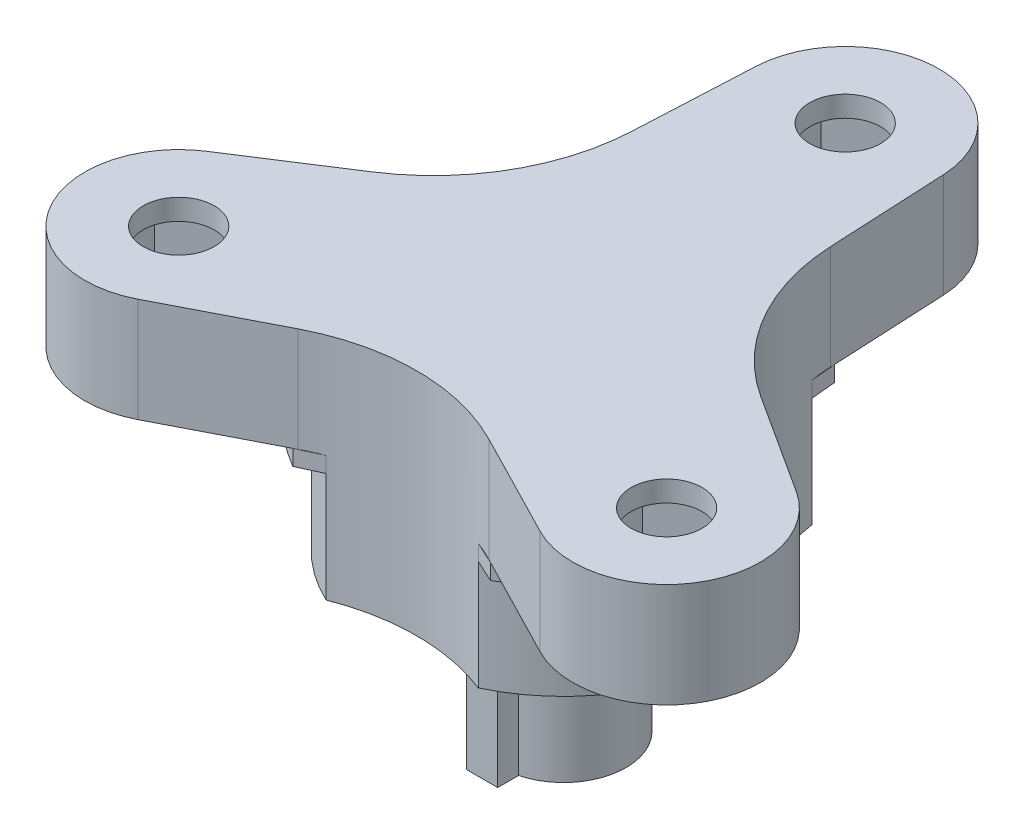
SolidWorks part; units mm, degrees
ref_plane "Ön Düzlem" through (0, 0, 0) normal (0, 0, 1) x (1, 0, 0)
ref_plane "Üst Düzlem" through (0, 0, 0) normal (0, 1, 0) x (1, 0, 0)
ref_plane "Sağ Düzlem" through (0, 0, 0) normal (1, 0, 0) x (0, 0, -1)
sketch "Sketch1" plane through (0, 0, 0) normal (0, 1, 0) x (1, 0, 0)
  line L0 (-4.4946, 13.7195) -> (-4.7723, 8.0342)
  line L1 (0, 13.5) -> (0, 0) construction
  line L2 (4.4946, 13.7195) -> (4.7723, 8.0342)
  line L3 (9.6341, -10.7522) -> (4.5717, -8.15)
  line L4 (14.1287, -2.9673) -> (9.3439, 0.1158)
  line L5 (-14.1287, -2.9673) -> (-9.3439, 0.1158)
  line L6 (-9.6341, -10.7522) -> (-4.5717, -8.15)
  circle A1 centre (0, 13.5) radius 1.7
  arc A3 (4.4946, 13.7195) -> (-4.4946, 13.7195) centre (0, 13.5) ccw
  circle A5 centre (0, 13.5) radius 4.5 construction
  circle A6 centre (11.6913, -6.75) radius 1.7
  arc A7 (9.6341, -10.7522) -> (14.1287, -2.9673) centre (11.6913, -6.75) ccw
  circle A8 centre (-11.6913, -6.75) radius 1.7
  arc A9 (-14.1287, -2.9673) -> (-9.6341, -10.7522) centre (-11.6913, -6.75) ccw
  circle A10 centre (0, 0) radius 5.8 construction
  arc A11 (-4.5717, -8.15) -> (4.5717, -8.15) centre (0, -17.0438) cw
  arc A12 (9.3439, 0.1158) -> (4.7723, 8.0342) centre (14.7604, 8.5219) cw
  arc A13 (-4.7723, 8.0342) -> (-9.3439, 0.1158) centre (-14.7604, 8.5219) cw
  point P27 (5.0229, 2.9)
  point P30 (0, 0)
  point P32 (-5.0229, 2.9)
  dimension "D2" = 3.4
  dimension "D3" = 11.6
  dimension "D7" = 10
  dimension "D4" = 4.5
  dimension "D1" = 13.5
  dimension "D6" = 3
extrude "Boss-Extrude1" add sketch "Sketch1" along normal blind 5
sketch "Sketch2" plane through (0, 5, 0) normal (0, 1, 0) x (1, 0, 0)
  line L0 (14.4413, -8.3377) -> (14.4413, -5.1623)
  line L1 (0, 16.6754) -> (-2.75, 15.0877)
  line L2 (-2.75, 15.0877) -> (-2.75, 11.9123)
  line L3 (-2.75, 11.9123) -> (0, 10.3246)
  line L4 (0, 10.3246) -> (2.75, 11.9123)
  line L5 (2.75, 11.9123) -> (2.75, 15.0877)
  line L6 (2.75, 15.0877) -> (0, 16.6754)
  line L7 (14.4413, -5.1623) -> (11.6913, -3.5746)
  line L8 (11.6913, -3.5746) -> (8.9413, -5.1623)
  line L9 (8.9413, -5.1623) -> (8.9413, -8.3377)
  line L10 (8.9413, -8.3377) -> (11.6913, -9.9254)
  line L11 (11.6913, -9.9254) -> (14.4413, -8.3377)
  line L12 (-14.4413, -8.3377) -> (-11.6913, -9.9254)
  line L13 (-11.6913, -9.9254) -> (-8.9413, -8.3377)
  line L14 (-8.9413, -8.3377) -> (-8.9413, -5.1623)
  line L15 (-8.9413, -5.1623) -> (-11.6913, -3.5746)
  line L16 (-11.6913, -3.5746) -> (-14.4413, -5.1623)
  line L17 (-14.4413, -5.1623) -> (-14.4413, -8.3377)
  circle A0 centre (0, 13.5) radius 2.75 construction
  point P24 (0, 0)
  dimension "D1" = 5.5
  dimension "D2" = 3
extrude "Cut-Extrude1" cut sketch "Sketch2" along normal blind 4 from surface at -5 starting at face at (0, 0, 0)
sketch "Sketch3" plane through (0, 0, 0) normal (0, -1, 0) x (1, 0, 0)
  circle A0 centre (0, 0) radius 2.5 construction
  dimension "D1" = 5
sketch "Sketch4" plane through (0, 0, 0) normal (0, -1, 0) x (1, 0, 0)
  arc A0 (-4.873, -7.0254) -> (4.873, -7.0254) centre (0, 0) ccw
  arc A1 (-3.6477, 7.7328) -> (-8.5207, -0.7074) centre (0, 0) ccw
  arc A2 (8.5207, -0.7074) -> (3.6477, 7.7328) centre (0, 0) ccw
  arc A3 (-4.7723, -8.0342) -> (-9.3439, -0.1158) centre (-14.7604, -8.5219) ccw construction
  arc A4 (-4.5717, 8.15) -> (4.5717, 8.15) centre (0, 17.0438) ccw construction
  arc A5 (9.3439, -0.1158) -> (4.7723, -8.0342) centre (14.7604, -8.5219) ccw construction
  arc A6 (-4.873, -7.0254) -> (-8.5207, -0.7074) centre (-14.7604, -8.5219) ccw
  arc A7 (-3.6477, 7.7328) -> (3.6477, 7.7328) centre (0, 17.0438) ccw
  arc A8 (8.5207, -0.7074) -> (4.873, -7.0254) centre (14.7604, -8.5219) ccw
  dimension "D1" = 17.1
extrude "Boss-Extrude2" add sketch "Sketch4" along normal blind 6
sketch "Sketch5" plane through (0, 0, 0) normal (0, -1, 0) x (1, 0, 0)
  line L0 (-9.6341, 10.7522) -> (-4.5717, 8.15) construction
  line L1 (-9.3439, -0.1158) -> (-14.1287, 2.9673) construction
  line L2 (-9.5, -0.0152) -> (-8.5207, -0.7074)
  line L3 (-4.7368, 8.2349) -> (-3.6477, 7.7328)
  line L4 (9.5, -0.0152) -> (8.5207, -0.7074)
  line L5 (4.7368, 8.2349) -> (3.6477, 7.7328)
  line L6 (-4.7632, -8.2196) -> (-4.873, -7.0254)
  line L7 (4.7632, -8.2196) -> (4.873, -7.0254)
  arc A0 (-4.873, -7.0254) -> (4.873, -7.0254) centre (0, 0) ccw construction
  arc A1 (8.5207, -0.7074) -> (3.6477, 7.7328) centre (0, 0) ccw construction
  arc A2 (-3.6477, 7.7328) -> (-8.5207, -0.7074) centre (0, 0) ccw construction
  arc A3 (-4.873, -7.0254) -> (4.873, -7.0254) centre (0, 0) ccw
  arc A4 (8.5207, -0.7074) -> (3.6477, 7.7328) centre (0, 0) ccw
  arc A5 (-3.6477, 7.7328) -> (-8.5207, -0.7074) centre (0, 0) ccw
  arc A6 (-4.7368, 8.2349) -> (-9.5, -0.0152) centre (0, 0) ccw
  arc A7 (9.5, -0.0152) -> (4.7368, 8.2349) centre (0, 0) ccw
  arc A8 (-4.7632, -8.2196) -> (4.7632, -8.2196) centre (0, 0) ccw
  point P24 (0, 0)
  dimension "D1" = 9.5
extrude "Boss-Extrude3" add sketch "Sketch5" along normal blind 0.75
sketch "Sketch6" plane through (0, -6, 0) normal (0, -1, 0) x (1, 0, 0)
  line L0 (-0.75, 2.9047) -> (-0.75, 3.9047)
  line L1 (0.75, 2.9047) -> (0.75, 3.9047)
  line L2 (-0.75, 3.4047) -> (0.75, 3.4047) construction
  line L3 (-0.75, 3.9047) -> (0.75, 3.9047)
  arc A0 (-0.75, 2.9047) -> (0.75, 2.9047) centre (0, 0) ccw
  point P9 (0, 3.4047)
  dimension "D1" = 6
  dimension "D2" = 1.5
  dimension "D3" = 1
extrude "Boss-Extrude4" add sketch "Sketch6" along normal blind 7.5
sketch "Sketch7" plane through (0, -13.5, 0) normal (0, -1, 0) x (1, 0, 0)
  circle A2 centre (0, 0) radius 1.3
  dimension "D1" = 2.6
extrude "Cut-Extrude2" cut sketch "Sketch7" against normal up to surface (7.5 mm away) up to face at (0, -6, 1.9286)
